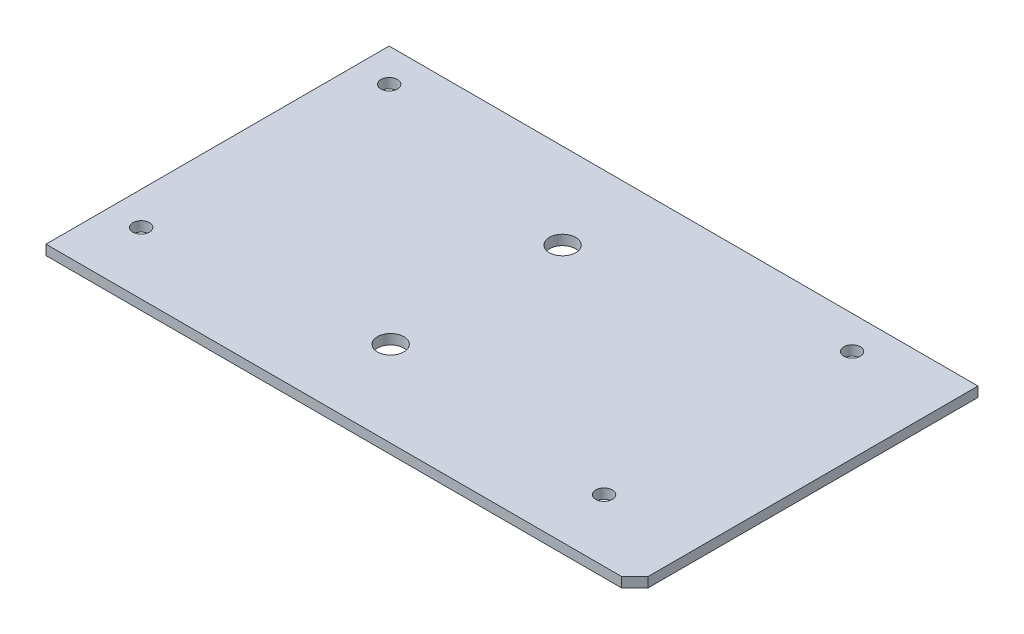
SolidWorks part; units mm, degrees
ref_plane "Front Plane" through (0, 0, 0) normal (0, 0, 1) x (1, 0, 0)
ref_plane "Top Plane" through (0, 0, 0) normal (0, 1, 0) x (1, 0, 0)
ref_plane "Right Plane" through (0, 0, 0) normal (1, 0, 0) x (0, 0, -1)
sketch "Sketch2" plane through (0, 0, 0) normal (0, 1, 0) x (1, 0, 0)
  line L0 (70, -37.5) -> (70, -56.28) construction
  line L1 (-70, 37.5) -> (70, 37.5) construction
  line L2 (-70, 37.5) -> (-70, -37.5) construction
  line L3 (-70, -37.5) -> (70, -37.5) construction
  line L4 (70, 37.5) -> (70, -37.5) construction
  line L5 (0, -37.5) -> (0, 37.5) construction
  line L6 (-70, 0) -> (70, 0) construction
  line L7 (70, 0) -> (98.09, 0) construction
  line L8 (-70, -37.5) -> (-80, -37.5) construction
  line L9 (-70, 37.5) -> (-70, 47.5) construction
  line L10 (-80, -37.5) -> (-80, -56.28)
  line L11 (-80, -56.28) -> (98.09, -56.28)
  line L12 (98.09, -56.28) -> (98.09, 47.5)
  line L13 (98.09, 47.5) -> (-80, 47.5)
  line L14 (-80, 47.5) -> (-80, -37.5)
  circle A0 centre (-70, -37.5) radius 2.5
  circle A1 centre (-70, 37.5) radius 2.5
  circle A2 centre (70, 37.5) radius 2.5
  circle A3 centre (70, -37.5) radius 2.5
  point P0 (0, 0)
  dimension "D7" = 5
  dimension "D1" = 140
  dimension "D2" = 75
  dimension "D3" = 18.78
  dimension "D4" = 28.09
  dimension "D5" = 10
  dimension "D6" = 10
extrude "Boss-Extrude1" add sketch "Sketch2" along normal blind 3
sketch "Sketch3" plane through (0, 3, 0) normal (0, 1, 0) x (1, 0, 0)
  line L0 (98.09, -56.28) -> (94.09, -56.28)
  line L1 (94.09, -56.28) -> (98.09, -52.28)
  line L2 (98.09, -56.28) -> (98.09, 47.5) construction
  line L3 (98.09, -52.28) -> (98.09, -56.28)
  dimension "D1" = 4
  dimension "D2" = 4
extrude "Cut-Extrude1" cut sketch "Sketch3" against normal through all
sketch "Sketch4" plane through (0, 3, 0) normal (0, 1, 0) x (1, 0, 0)
  circle A0 centre (-1.66, 21.61) radius 4
  circle A1 centre (-1.66, -30.39) radius 4
  circle A2 centre (-70, 37.5) radius 2.5 construction
  dimension "D1" = 8
  dimension "D2" = 8
  dimension "D3" = 68.34
  dimension "D4" = 15.89
  dimension "D5" = 52
extrude "Cut-Extrude2" cut sketch "Sketch4" against normal blind 5
